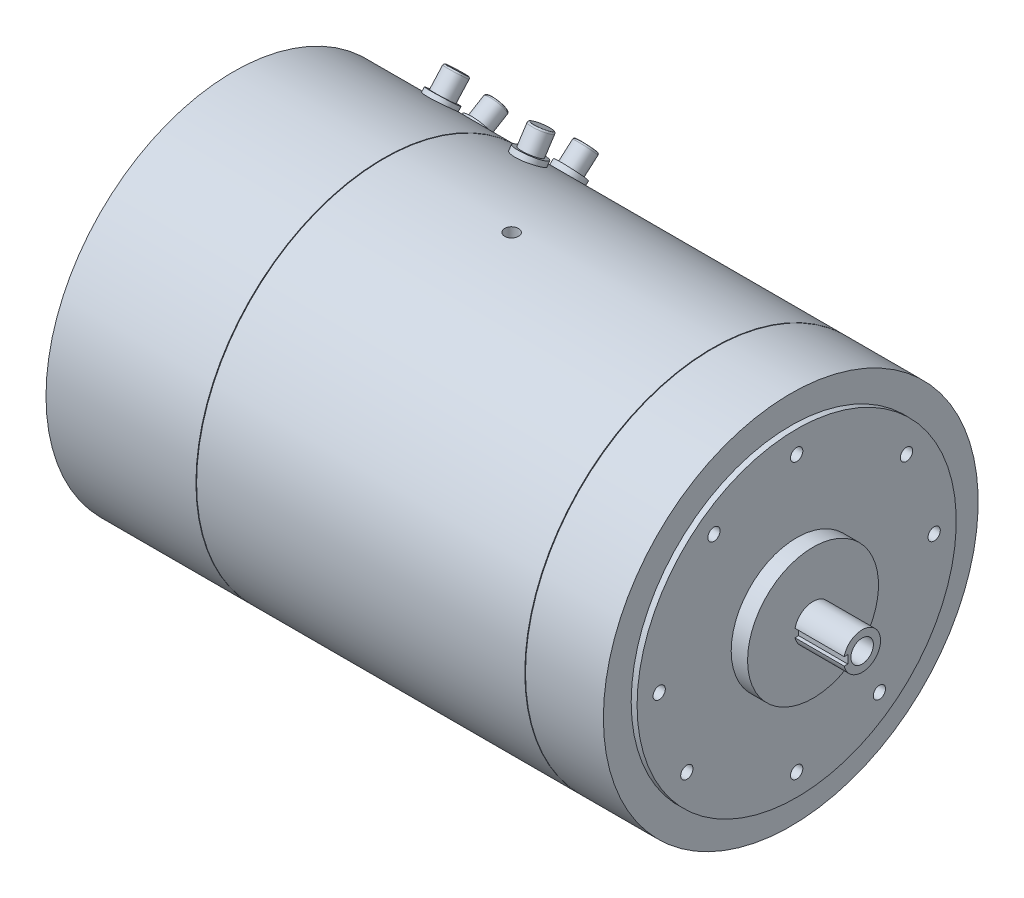
SolidWorks part; units mm, degrees
material "Cast Alloy Steel"
ref_plane "Front Plane" through (0, 0, 0) normal (0, 0, 1) x (1, 0, 0)
ref_plane "Top Plane" through (0, 0, 0) normal (0, 1, 0) x (1, 0, 0)
ref_plane "Right Plane" through (0, 0, 0) normal (1, 0, 0) x (0, 0, -1)
sketch "Sketch2" plane through (0, 0, 0) normal (0, 0, 1) x (1, 0, 0)
  line L0 (-32.8723, 0) -> (585.553, 0) construction
  line L2 (516.6614, 50.8) -> (516.6614, 14.2875)
  line L3 (516.6614, 50.8) -> (503.9614, 50.8)
  line L4 (503.9614, 50.8) -> (503.9614, 123.825)
  line L5 (503.9614, 123.825) -> (499.3894, 123.825)
  line L6 (499.3894, 123.825) -> (499.3894, 145.415)
  line L7 (499.3894, 145.415) -> (438.9374, 145.415)
  line L8 (66.9036, 145.415) -> (66.9036, 101.6)
  line L9 (66.9036, 101.6) -> (60.452, 101.6)
  line L10 (60.452, 101.6) -> (60.452, 36.83)
  line L11 (60.452, 36.83) -> (57.404, 36.83)
  line L12 (516.6614, 14.2875) -> (554.7614, 14.2875)
  line L13 (554.7614, 14.2875) -> (554.7614, 0)
  line L14 (57.404, 36.83) -> (57.404, 11.1125)
  line L15 (57.404, 11.1125) -> (0, 11.1125)
  line L16 (0, 11.1125) -> (0, 0)
  line L17 (554.7614, 0) -> (0, 0)
  line L18 (438.9374, 145.415) -> (438.9374, 142.875)
  line L19 (438.9374, 142.875) -> (438.4294, 142.875)
  line L20 (438.4294, 142.875) -> (438.4294, 145.415)
  line L21 (183.2356, 145.415) -> (183.2356, 142.875)
  line L22 (183.2356, 142.875) -> (183.7436, 142.875)
  line L23 (183.7436, 142.875) -> (183.7436, 145.415)
  line L24 (438.4294, 145.415) -> (183.7436, 145.415)
  line L25 (183.2356, 145.415) -> (66.9036, 145.415)
  dimension "D1" = 554.7614
  dimension "D2" = 28.575
  dimension "D3" = 38.1
  dimension "D4" = 50.8
  dimension "D5" = 55.372
  dimension "D6" = 432.4858
  dimension "D7" = 57.404
  dimension "D8" = 60.452
  dimension "D9" = 66.9036
  dimension "D10" = 22.225
  dimension "D11" = 290.83
  dimension "D12" = 247.65
  dimension "D13" = 101.6
  dimension "D14" = 73.66
  dimension "D15" = 203.2
  dimension "D16" = 0.508
  dimension "D17" = 60.96
  dimension "D18" = 2.54
  dimension "D19" = 0.508
  dimension "D21" = 116.84
revolve "Revolve1" add sketch "Sketch2" angle 360 about L0
sketch "Sketch4" plane through (503.9614, 0, 0) normal (1, 0, 0) x (0, 0, -1)
  line L0 (-106.68, 0) -> (106.68, 0) construction
  line L1 (0, 158.7765) -> (0, -158.8846) construction
  line L2 (-85.1984, -64.2016) -> (85.1984, 64.2016) construction
  line L3 (0, 0) -> (64.2016, -85.1984) construction
  circle A0 centre (0, 0) radius 106.68 construction
  circle A1 centre (106.68, 0) radius 4.7625
  circle A2 centre (85.1984, 64.2016) radius 4.7625
  circle A3 centre (0, -106.68) radius 4.7625
  circle A4 centre (64.2016, -85.1984) radius 4.7625
  circle A5 centre (-106.68, 0) radius 4.7625
  circle A6 centre (-85.1984, -64.2016) radius 4.7625
  circle A7 centre (0, 106.68) radius 4.7625
  circle A8 centre (-64.2016, 85.1984) radius 4.7625
  dimension "D1" = 213.36
  dimension "D2" = 9.525
  dimension "D3" = 37
  dimension "D4" = 213.36
  dimension "D5" = 53
extrude "Output mount holes" cut sketch "Sketch4" against normal blind 20.32
sketch "Sketch5" plane through (60.452, 0, 0) normal (-1, 0, 0) x (0, 0, 1)
  line L0 (0, 0) -> (160.8554, 0) construction
  line L1 (0, 0) -> (74.5348, 15.8429) construction
  line L2 (0, 0) -> (63.9067, -41.5015) construction
  circle A0 centre (0, 0) radius 76.2 construction
  circle A1 centre (74.5348, 15.8429) radius 3.9688
  circle A2 centre (63.9067, -41.5015) radius 3.9688
  circle A3 centre (15.8429, -74.5348) radius 3.9688
  circle A4 centre (-41.5015, -63.9067) radius 3.9688
  circle A5 centre (-74.5348, -15.8429) radius 3.9688
  circle A6 centre (-63.9067, 41.5015) radius 3.9687
  circle A7 centre (-15.8429, 74.5348) radius 3.9688
  circle A8 centre (41.5015, 63.9067) radius 3.9687
  dimension "D1" = 152.4
  dimension "D2" = 7.9375
  dimension "D3" = 12
extrude "Aux output mount holes" cut sketch "Sketch5" against normal blind 25.4
sketch "Sketch10" plane through (554.7614, 0, 0) normal (1, 0, 0) x (0, 0, -1)
  circle A0 centre (0, 0) radius 8.7376
  dimension "D1" = 17.4752
extrude "Pilot Hole" cut sketch "Sketch10" against normal blind 19.05
hole_wizard "5/16-18 Tapped Hole4" positions "3DSketch3" profile "Sketch12" tap size "5/16-18" standard "Ansi Inch"
sketch3d "3DSketch3"
  circle A0 centre (554.7614, 0, 0) radius 8.7376 construction
  point P0 (535.7114, 0, 0)
  point P8 (563.499, 0, 0)
sketch "Sketch12" plane through (535.7114, 0, 0) normal (0, 1, 0) x (0, 0, -1)
  line L0 (0, 0) -> (0, 34.4223)
  line L1 (0, 34.4223) -> (3.2639, 32.4612)
  line L2 (3.2639, 32.4612) -> (3.2639, 0)
  line L5 (3.2639, 0) -> (0, 0)
  line L10 (0, 34.4223) -> (-3.2639, 32.4612) construction
  line L11 (0, -6.35) -> (0, 107.95) construction
  dimension "Tap Drill Dia." = 6.5278
  dimension "Tap Drill Depth" = 32.4612
  dimension "Drill Angle" = 118
ref_plane "DE Keyway Plane" through (0, 0, 11.1125) normal (0, 0, 1) x (1, 0, 0)
sketch "Sketch13" plane through (0, 0, 11.1125) normal (0, 0, 1) x (1, 0, 0)
  line L0 (527.0865, 0) -> (592.7369, 0) construction
  line L1 (554.7614, -3.175) -> (554.7614, 3.175)
  line L2 (554.7614, -14.2875) -> (554.7614, 14.2875) construction
  line L3 (554.7614, 3.175) -> (516.6614, 3.175)
  line L4 (516.6614, 3.175) -> (516.6614, -3.175)
  line L6 (554.7614, -3.175) -> (516.6614, -3.175)
  point P12 (554.7614, 0)
  dimension "D1" = 38.1
  dimension "D2" = 6.35
extrude "Drive End Keyway" cut sketch "Sketch13" along normal blind 19.05
hole_wizard "1/4-20 Tapped Hole1" positions "Sketch15" profile "Sketch14" tap size "1/4-20" standard "Ansi Inch"
sketch "Sketch15" plane through (0, 0, 0) normal (-1, 0, 0) x (0, 0, 1)
  point P0 (0, 0)
sketch "Sketch14" plane through (0, 0, 0) normal (0, 1, 0) x (0, 0, 1)
  line L0 (0, 0) -> (0, 26.9338)
  line L1 (0, 26.9338) -> (2.5527, 25.4)
  line L2 (2.5527, 25.4) -> (2.5527, 0)
  line L5 (2.5527, 0) -> (0, 0)
  line L10 (0, 26.9338) -> (-2.5527, 25.4) construction
  line L11 (0, -6.35) -> (0, 107.95) construction
  dimension "Tap Drill Dia." = 5.1054
  dimension "Tap Drill Depth" = 25.4
  dimension "Drill Angle" = 118
ref_plane "CE Keyway Plane" through (0, 0, 8.4709) normal (0, 0, 1) x (1, 0, 0)
sketch "Sketch16" plane through (0, 0, 8.4709) normal (0, 0, 1) x (1, 0, 0)
  line L0 (0, 11.1125) -> (0, -11.1125) construction
  line L1 (0, 2.3876) -> (50.8, 2.3876)
  line L2 (0, 2.3876) -> (0, -2.3876)
  line L3 (0, -2.3876) -> (50.8, -2.3876)
  line L4 (50.8, 2.3876) -> (50.8, -2.3876)
  dimension "D1" = 50.8
  dimension "D2" = 4.7752
extrude "CE Keyway" cut sketch "Sketch16" along normal blind 19.05
ref_plane "A1 Base Plane" through (0, 0, 0) normal (0, -0.7431, 0.6691) x (1, 0, 0)
ref_plane "A1 Plane" through (0, 103.8173, -93.4775) normal (0, -0.7431, 0.6691) x (-1, 0, 0)
sketch "Sketch17" plane through (0, 103.8173, -93.4775) normal (0, -0.7431, 0.6691) x (-1, 0, 0)
  line L0 (0, 0) -> (226.8096, 0) construction
  line L1 (-66.9036, -145.415) -> (-66.9036, 145.415) construction
  circle A0 centre (-129.8956, 0) radius 8.255
  dimension "D3" = 16.51
  dimension "D1" = 62.992
extrude "A1 Post" add sketch "Sketch17" against normal blind 25.4
sketch "Sketch19" plane through (0, 103.8173, -93.4775) normal (0, -0.7431, 0.6691) x (-1, 0, 0)
  circle A0 centre (-129.8956, 0) radius 11.43
extrude "A1 Base" add sketch "Sketch19" against normal blind 8.89
fillet "A1 Fillet" radius 1.27 1 edges at (129.8956, 117.1695, -116.6081)
pattern_circular "A2 Connector" count 2 over 17 about axis through (-32.8723, 0, 0) along (-1, 0, 0) of "A1 Post", "A1 Base", "A1 Fillet"
ref_plane "S1 Base Plane" through (0, 0, 0) normal (0, -0.6561, 0.7547) x (1, 0, 0)
ref_plane "S1 Plane" through (0, 91.6514, -105.4329) normal (0, -0.6561, 0.7547) x (1, 0, 0)
sketch "Sketch20" plane through (0, 91.6514, -105.4329) normal (0, -0.6561, 0.7547) x (1, 0, 0)
  line L0 (0, 0) -> (604.3276, 0) construction
  line L1 (438.4294, 0) -> (183.7436, 0) construction
  line L2 (66.9036, 145.415) -> (66.9036, -145.415) construction
  circle A0 centre (216.2556, 0) radius 8.255
  dimension "D1" = 16.51
  dimension "D2" = 149.352
extrude "S1 Post" add sketch "Sketch20" against normal blind 25.4
sketch "Sketch21" plane through (0, 91.6514, -105.4329) normal (0, -0.6561, 0.7547) x (1, 0, 0)
  circle A0 centre (216.2556, 0) radius 11.43
  dimension "D1" = 22.86
extrude "S1 Base" add sketch "Sketch21" against normal blind 9.525
fillet "S1 Fillet" radius 1.27 1 edges at (216.2556, 102.0852, -130.0183)
pattern_circular "S2 Connector" count 2 over 16 about axis through (-32.8723, 0, 0) along (-1, 0, 0) of "S1 Base", "S1 Post", "S1 Fillet"
ref_plane "Lifting Hole Plane" through (0, 145.415, 0) normal (0, 1, 0) x (-1, 0, 0)
hole_wizard "Lifting Hole" positions "Sketch26" profile "Sketch25" tap size "1/2-13" standard "Ansi Inch"
sketch "Sketch26" plane through (0, 145.415, 0) normal (0, 1, 0) x (-1, 0, 0)
  line L0 (0, 0) -> (-290.2688, 0) construction
  line L3 (-66.9036, -145.415) -> (-66.9036, 145.415) construction
  point P10 (-282.8036, 0)
  dimension "D1" = 215.9
sketch "Sketch25" plane through (282.8036, 145.415, 0) normal (1, 0, 0) x (0, 0, 1)
  line L0 (0, 0) -> (0, 38.3985)
  line L1 (0, 38.3985) -> (5.3581, 35.179)
  line L2 (5.3581, 35.179) -> (5.3581, 0)
  line L5 (5.3581, 0) -> (0, 0)
  line L10 (0, 38.3985) -> (-5.3581, 35.179) construction
  line L11 (0, -6.35) -> (0, 107.95) construction
  dimension "Tap Drill Dia." = 10.7163
  dimension "Tap Drill Depth" = 35.179
  dimension "Drill Angle" = 118
pattern_circular "Lifting Hole 2" count 2 over 90 about axis through (-32.8723, 0, 0) along (-1, 0, 0) of "Lifting Hole"
